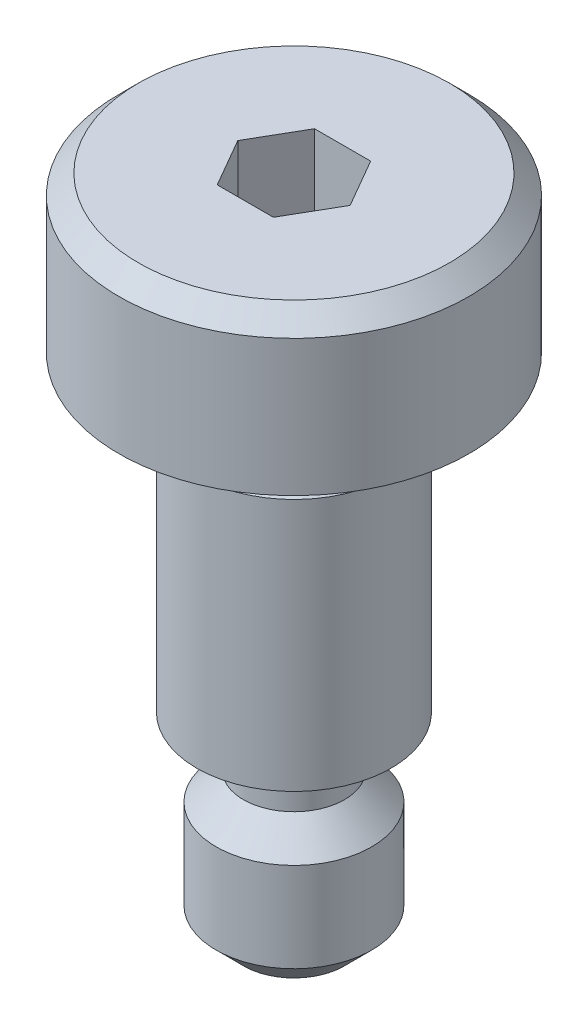
SolidWorks part; units mm, degrees
ref_plane "Front plane" through (0, 0, 0) normal (0, 0, 1) x (1, 0, 0)
ref_plane "Top plane" through (0, 0, 0) normal (0, 1, 0) x (1, 0, 0)
ref_plane "Right Plane" through (0, 0, 0) normal (1, 0, 0) x (0, 0, -1)
sketch "Sketch1" plane through (0, 0, 0) normal (0, 0, 1) x (1, 0, 0)
  line L0 (0, 0) -> (0, 17)
  line L1 (0, 17) -> (4, 17)
  line L2 (4, 17) -> (4.5, 16.5)
  line L3 (4.5, 16.5) -> (4.5, 13)
  line L4 (4.5, 13) -> (2.5, 13)
  line L5 (2, 12.5) -> (2, 12)
  line L6 (2, 12) -> (2.5, 11.5)
  line L7 (2.5, 11.5) -> (2.5, 5)
  line L8 (2.5, 5) -> (2, 5)
  line L9 (1.3, 4.3) -> (1.3, 3.7)
  line L10 (1.3, 3.7) -> (2, 3)
  line L11 (2, 3) -> (2, 0.7)
  line L12 (2, 0.7) -> (1.3, 0)
  line L13 (1.3, 0) -> (0, 0)
  arc A0 (2.5, 13) -> (2, 12.5) centre (2.5, 12.5) ccw
  arc A1 (2, 5) -> (1.3, 4.3) centre (2, 4.3) ccw
  dimension "D9" = 1.5
  dimension "D1" = 2
  dimension "D2" = 4.5
  dimension "D3" = 2.5
  dimension "D4" = 4
  dimension "D5" = 135
  dimension "D6" = 0.5
  dimension "D7" = 8
  dimension "D8" = 0.5
  dimension "D10" = 0.7
  dimension "D11" = 5
  dimension "D12" = 2
revolve "Revolve1" add sketch "Sketch1" angle 360 about L0
sketch "Sketch2" plane through (0, 17, 0) normal (0, 1, 0) x (1, 0, 0)
  line L1 (0.7217, 1.25) -> (-0.7217, 1.25)
  line L2 (-0.7217, 1.25) -> (-1.4434, 0)
  line L3 (-1.4434, 0) -> (-0.7217, -1.25)
  line L4 (-0.7217, -1.25) -> (0.7217, -1.25)
  line L5 (0.7217, -1.25) -> (1.4434, 0)
  line L6 (1.4434, 0) -> (0.7217, 1.25)
  circle A0 centre (0, 0) radius 1.25 construction
  dimension "D1" = 2.5
extrude "Cut-Extrude1" cut sketch "Sketch2" against normal blind 3
